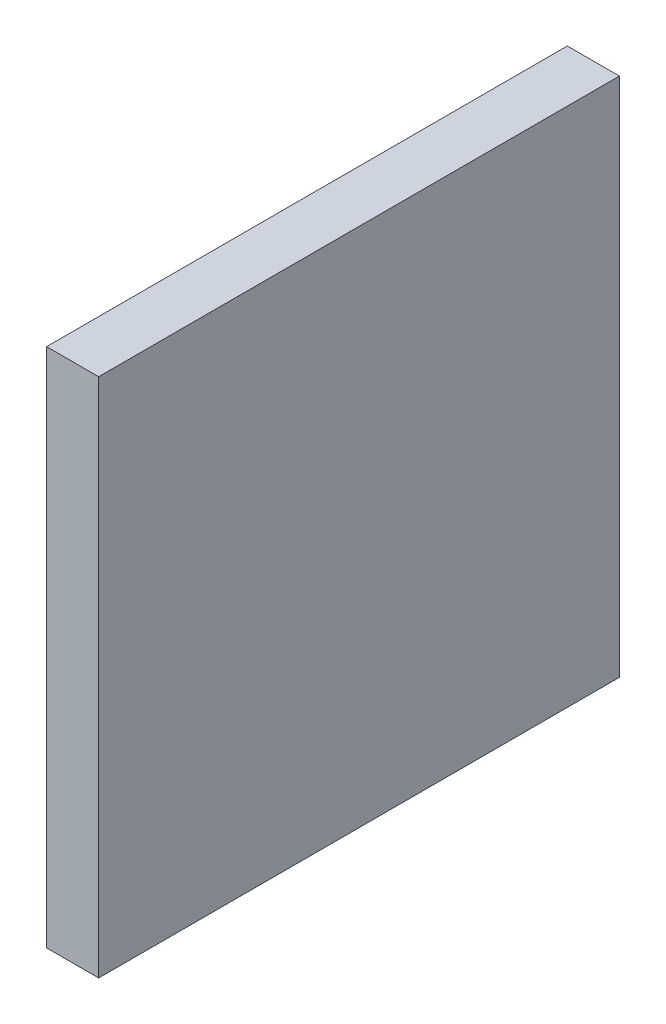
SolidWorks part; units mm, degrees
ref_plane "Front Plane" through (0, 0, 0) normal (0, 0, 1) x (1, 0, 0)
ref_plane "Top Plane" through (0, 0, 0) normal (0, 1, 0) x (1, 0, 0)
ref_plane "Right Plane" through (0, 0, 0) normal (1, 0, 0) x (0, 0, -1)
sketch "Sketch2" plane through (0, 0, 0) normal (1, 0, 0) x (0, 0, -1)
  line L1 (-25, -25) -> (25, -25)
  line L2 (-25, -25) -> (-25, 25)
  line L3 (-25, 25) -> (25, 25)
  line L4 (25, -25) -> (25, 25)
  line L5 (-25, -25) -> (25, 25) construction
  line L6 (-25, 25) -> (25, -25) construction
  point P0 (0, 0)
  dimension "D1" = 50
  dimension "D2" = 50
extrude "Boss-Extrude1" add sketch "Sketch2" along normal blind 5
